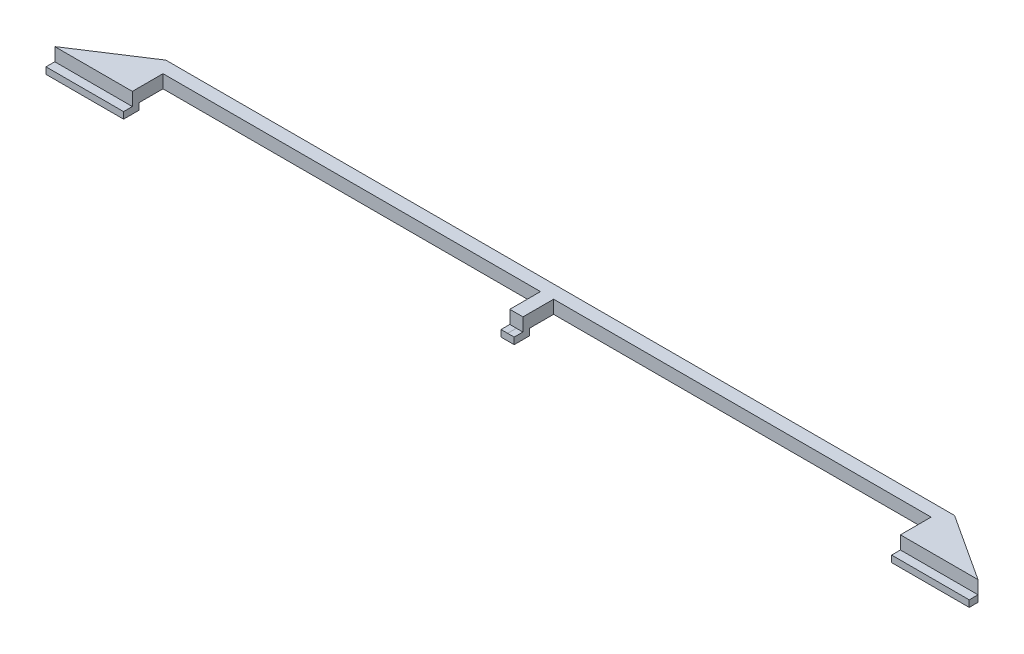
SolidWorks part; units mm, degrees
ref_plane "Front Plane" through (0, 0, 0) normal (0, 0, 1) x (1, 0, 0)
ref_plane "Top Plane" through (0, 0, 0) normal (0, 1, 0) x (1, 0, 0)
ref_plane "Right Plane" through (0, 0, 0) normal (1, 0, 0) x (0, 0, -1)
sketch "Sketch1" plane through (0, 0, 0) normal (0, 1, 0) x (1, 0, 0)
  line L1 (450, 15) -> (-450, 15)
  line L2 (450, 15) -> (450, -15)
  line L3 (450, -15) -> (-450, -15)
  line L4 (-450, 15) -> (-450, -15)
  line L5 (450, 15) -> (-450, -15) construction
  line L6 (450, -15) -> (-450, 15) construction
  point P0 (0, 0)
  dimension "D1" = 30
  dimension "D2" = 900
extrude "Boss-Extrude1" add sketch "Sketch1" along normal blind 30
sketch "Sketch2" plane through (0, 30, 0) normal (0, 1, 0) x (1, 0, 0)
  line L0 (-450, 15) -> (-603.4968, -85)
  line L1 (-603.4968, -85) -> (-426.4491, -85)
  line L2 (-426.4491, -85) -> (-426.4491, 15)
  line L3 (450, 15) -> (-450, 15) construction
  line L4 (-426.4491, 15) -> (-450, 15)
  line L6 (450, 15) -> (450, -85)
  line L7 (450, -85) -> (435, -85)
  line L8 (435, -85) -> (435, 15)
  line L9 (435, 15) -> (450, 15)
  dimension "D1" = 15
  dimension "D2" = 100
  dimension "D3" = 23.5509
extrude "Boss-Extrude2" add sketch "Sketch2" against normal blind 30
sketch "Sketch3" plane through (0, 30, 0) normal (0, 1, 0) x (1, 0, 0)
  line L0 (-603.4968, -85) -> (-580.4723, -70)
  line L1 (-450, 15) -> (-603.4968, -85) construction
  line L2 (-580.4723, -70) -> (-426.4491, -70)
  line L3 (-426.4491, -85) -> (-426.4491, -15) construction
  line L4 (-426.4491, -70) -> (-426.4491, -85)
  line L5 (-426.4491, -85) -> (-603.4968, -85)
  line L6 (450, -85) -> (435, -85)
  line L7 (435, -15) -> (435, -85) construction
  line L8 (435, -85) -> (435, -70)
  line L9 (435, -70) -> (450, -70)
  line L10 (450, -85) -> (450, 15) construction
  line L11 (450, -70) -> (450, -85)
  dimension "D1" = 15
extrude "Boss-Extrude3" add sketch "Sketch3" along normal blind 15
sketch "Sketch4" plane through (0, 0, 85) normal (0, 0, 1) x (1, 0, 0)
  line L0 (-603.4968, 45) -> (-426.4491, 45)
  line L1 (-426.4491, 45) -> (-426.4491, 30)
  line L3 (-426.4491, 30) -> (-603.4968, 30)
  line L5 (-603.4968, 30) -> (-603.4968, 45)
  line L6 (435, 45) -> (450, 45)
  line L7 (450, 45) -> (450, 30)
  line L8 (450, 30) -> (435, 29.8945)
  line L9 (435, 0) -> (435, 45) construction
  line L10 (435, 29.8945) -> (435, 45)
  dimension "D1" = 15
  dimension "D2" = 15
extrude "Boss-Extrude4" add sketch "Sketch4" along normal blind 20
mirror "Mirror1" about plane through (450, 30, -15) normal (-1, 0, 0) of bodies 104
mirror "Mirror3" about plane through (0, 45, 0) normal (0, -1, 0)
sketch "Sketch5" plane through (0, 0, 0) normal (0, -1, 0) x (-1, 0, 0)
  line L0 (-465, -15) -> (-465, -85) construction
  line L1 (-1649.2777, -413.505) -> (719.2777, -413.505)
  line L2 (-1649.2777, -413.505) -> (-1649.2777, 313.505)
  line L3 (-1649.2777, 313.505) -> (719.2777, 313.505)
  line L4 (719.2777, -413.505) -> (719.2777, 313.505)
  line L5 (-1649.2777, -413.505) -> (719.2777, 313.505) construction
  line L6 (-1649.2777, 313.505) -> (719.2777, -413.505) construction
  point P0 (-465, -50)
extrude "Cut-Extrude1" cut sketch "Sketch5" against normal blind 45
